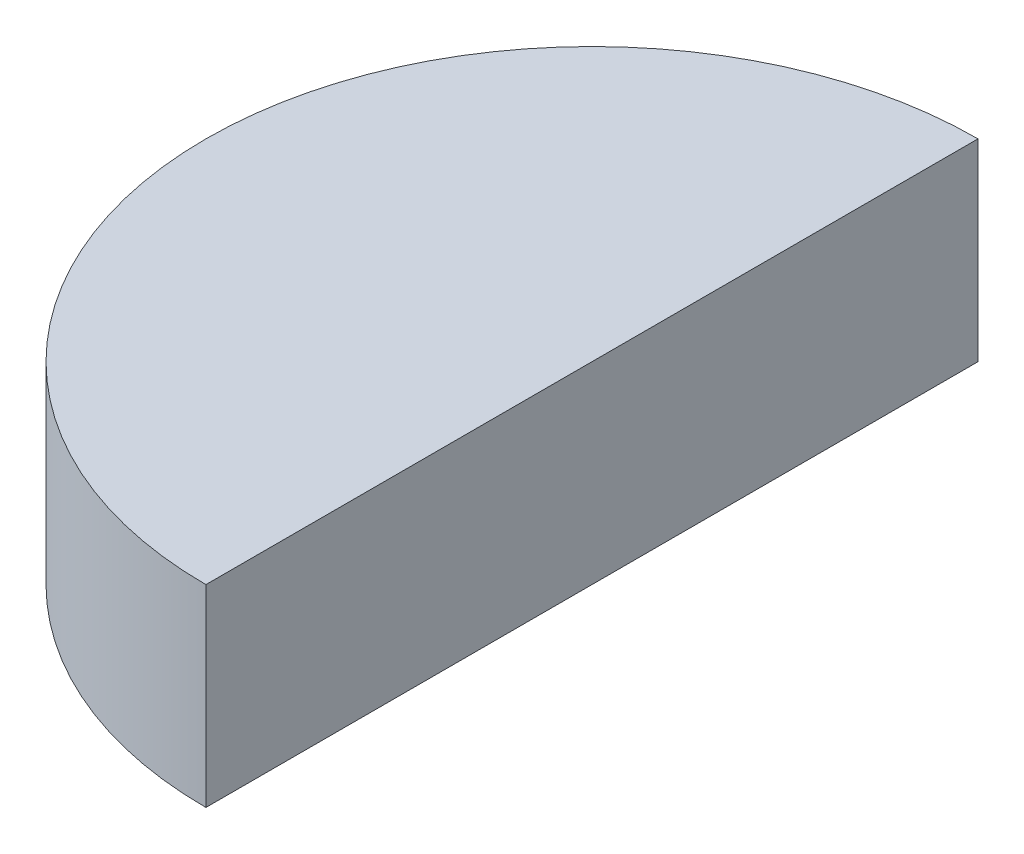
SolidWorks part; units mm, degrees
ref_plane "Front Plane" through (0, 0, 0) normal (0, 0, 1) x (1, 0, 0)
ref_plane "Top Plane" through (0, 0, 0) normal (0, 1, 0) x (1, 0, 0)
ref_plane "Right Plane" through (0, 0, 0) normal (1, 0, 0) x (0, 0, -1)
sketch "Sketch5" plane through (0, 0, 0) normal (1, 0, 0) x (0, 0, -1)
  line L1 (0, 0) -> (10000, 0)
  line L2 (0, 0) -> (0, 5000)
  line L3 (0, 5000) -> (10000, 5000)
  line L4 (10000, 0) -> (10000, 5000)
  dimension "D1" = 5000
  dimension "D2" = 10000
revolve "Revolve1" add sketch "Sketch5" angle 180 about L2
